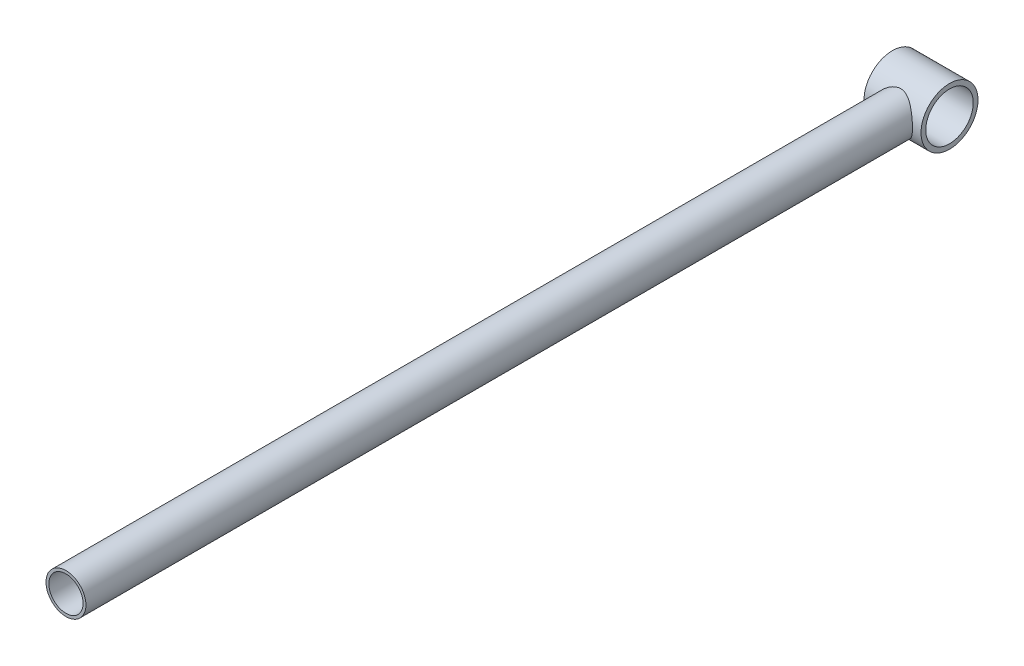
SolidWorks part; units mm, degrees
ref_plane "Спереди" through (0, 0, 0) normal (0, 0, 1) x (1, 0, 0)
ref_plane "Сверху" through (0, 0, 0) normal (0, 1, 0) x (1, 0, 0)
ref_plane "Справа" through (0, 0, 0) normal (1, 0, 0) x (0, 0, -1)
sketch "Эскиз1" plane through (0, 0, 0) normal (0, 0, 1) x (1, 0, 0)
  circle A0 centre (0, 0) radius 21
  dimension "D1" = 42
extrude "Бобышка-Вытянуть1" add sketch "Эскиз1" along normal blind 900
sketch "Эскиз2" plane through (0, 0, 0) normal (0, 0, -1) x (-1, 0, 0)
  circle A0 centre (0, 0) radius 18
  dimension "D1" = 36
extrude "Вырез-Вытянуть1" cut sketch "Эскиз2" against normal through all
sketch "Эскиз4" plane through (0, 0, 0) normal (1, 0, 0) x (0, 0, -1)
  circle A0 centre (0, 0) radius 30
  dimension "D1" = 60
extrude "Бобышка-Вытянуть2" add sketch "Эскиз4" along normal mid plane 60
sketch "Эскиз5" plane through (30, 0, 0) normal (1, 0, 0) x (0, 0, -1)
  circle A0 centre (0, 0) radius 25
  dimension "D1" = 50
extrude "Вырез-Вытянуть2" cut sketch "Эскиз5" against normal through all
